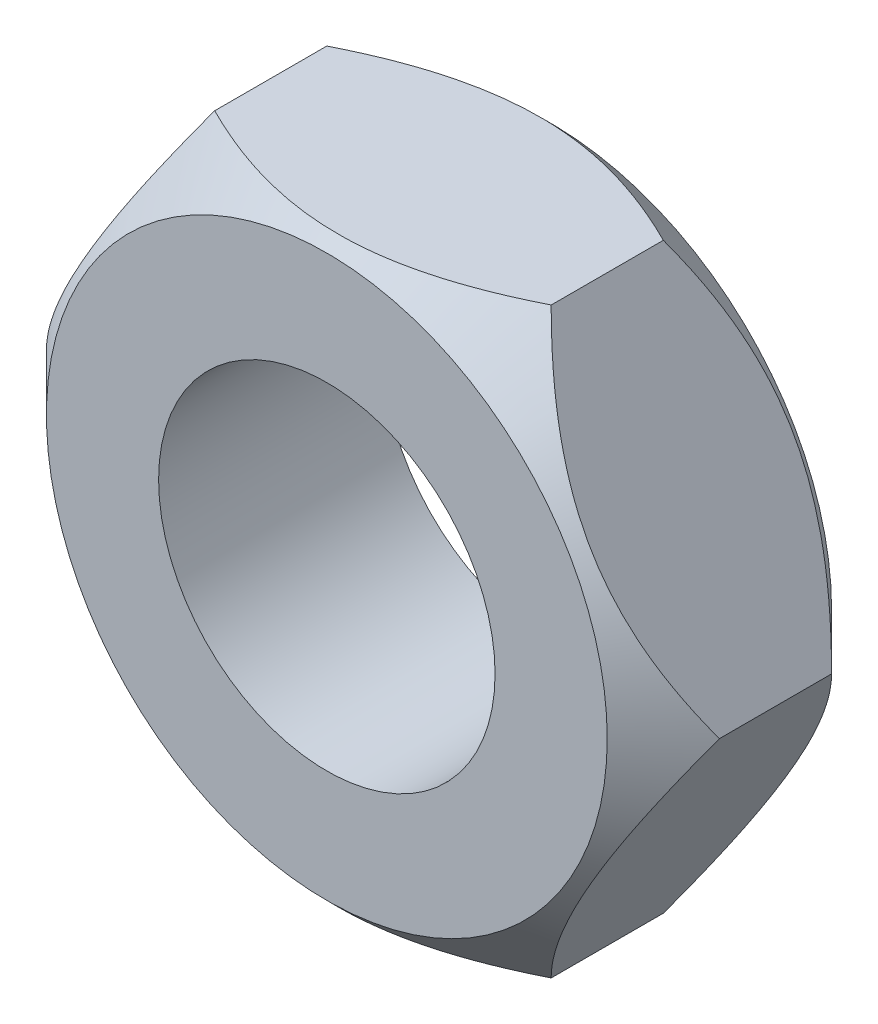
SolidWorks part; units mm, degrees
ref_plane "Front Plane" through (0, 0, 0) normal (0, 0, 1) x (1, 0, 0)
ref_plane "Top Plane" through (0, 0, 0) normal (0, 1, 0) x (1, 0, 0)
ref_plane "Right Plane" through (0, 0, 0) normal (1, 0, 0) x (0, 0, -1)
sketch "Sketch1" plane through (0, 0, 0) normal (0, 0, 1) x (1, 0, 0)
  line L1 (4.5, 7.7942) -> (-4.5, 7.7942)
  line L2 (-4.5, 7.7942) -> (-9, 0)
  line L3 (-9, 0) -> (-4.5, -7.7942)
  line L4 (-4.5, -7.7942) -> (4.5, -7.7942)
  line L5 (4.5, -7.7942) -> (9, 0)
  line L6 (9, 0) -> (4.5, 7.7942)
  circle A0 centre (0, 0) radius 7.7942 construction
  circle A1 centre (0, 0) radius 4.5
  dimension "D1" = 9
  dimension "D2" = 9
extrude "Boss-Extrude1" add sketch "Sketch1" along normal mid plane 6
sketch "Sketch4" plane through (0, 0, 3) normal (0, 0, 1) x (1, 0, 0)
  circle A0 centre (0, 0) radius 7.5
extrude "Cut-Extrude1" cut sketch "Sketch4" against normal blind 6 draft 45 flip side to cut
mirror "Mirror1" about plane through (0, 0, 0) normal (0, 0, 1) of "Cut-Extrude1"
